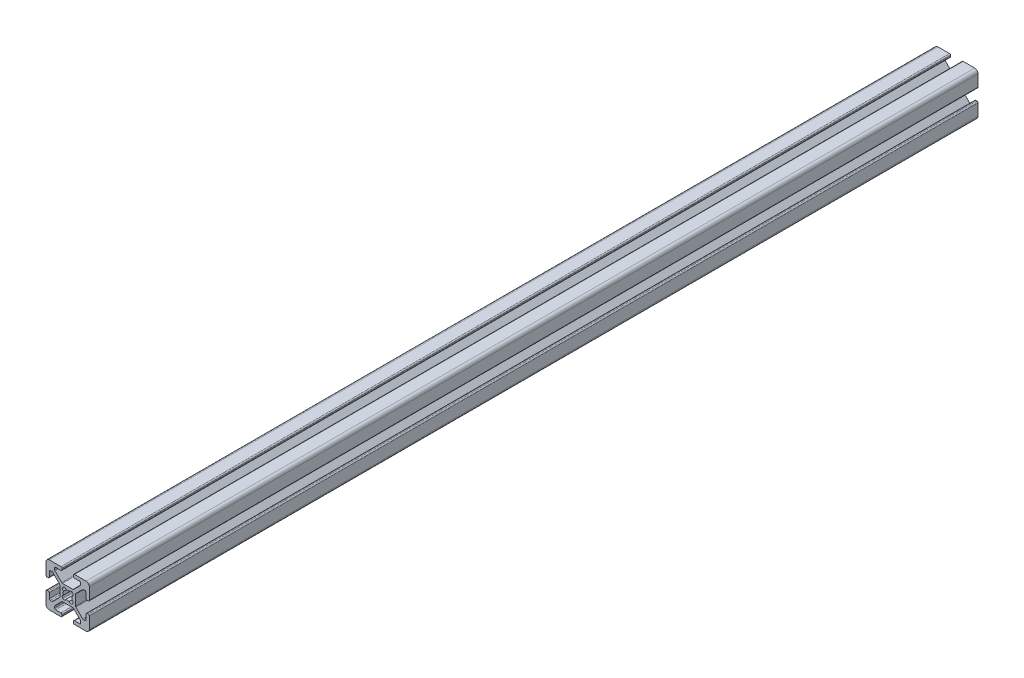
SolidWorks part; units mm, degrees
ref_plane "Front Plane" through (0, 0, 0) normal (0, 0, 1) x (1, 0, 0)
ref_plane "Top Plane" through (0, 0, 0) normal (0, 1, 0) x (1, 0, 0)
ref_plane "Right Plane" through (0, 0, 0) normal (1, 0, 0) x (0, 0, -1)
sketch "Sketch1" plane through (0, 0, 0) normal (0, 0, 1) x (1, 0, 0)
  line L0 (-5.0323, -0.3411) -> (-5.5163, -0.3411)
  line L1 (-6.0243, 0.1669) -> (-6.0243, 2.5159)
  line L2 (-4.5243, 0.1669) -> (-4.5243, 5.5289)
  line L3 (-10.8693, -5.355) -> (-10.8693, -0.5871)
  line L4 (-7.2582, 3.0239) -> (-6.5323, 3.0239)
  line L5 (-7.6174, 2.8752) -> (-10.7205, -0.2279)
  line L6 (-5.0323, -5.6011) -> (-5.5163, -5.6011)
  line L7 (-4.5243, -6.1091) -> (-4.5243, -11.4711)
  line L8 (-6.0243, -6.1091) -> (-6.0243, -8.4581)
  line L9 (-7.2582, -8.9661) -> (-6.5323, -8.9661)
  line L10 (-7.6174, -8.8173) -> (-10.7205, -5.7142)
  line L11 (-12.3994, -5.2756) -> (-12.2198, -5.096)
  line L12 (-17.1543, 6.5209) -> (-17.1543, 6.0369)
  line L13 (-17.6623, 7.0289) -> (-23.0243, 7.0289)
  line L14 (-17.6623, 5.5289) -> (-20.0113, 5.5289)
  line L15 (-12.1404, 0.6839) -> (-16.9082, 0.6839)
  line L16 (-20.5193, 4.295) -> (-20.5193, 5.0209)
  line L17 (-20.3705, 3.9358) -> (-17.2674, 0.8327)
  line L18 (-11.8943, 6.5209) -> (-11.8943, 6.0369)
  line L19 (-11.3863, 7.0289) -> (-6.0243, 7.0289)
  line L20 (-11.3863, 5.5289) -> (-9.0373, 5.5289)
  line L21 (-8.5293, 4.295) -> (-8.5293, 5.0209)
  line L22 (-8.6781, 3.9358) -> (-11.7812, 0.8327)
  line L23 (-12.2198, -0.8462) -> (-12.3994, -0.6666)
  line L24 (-24.0163, -5.6011) -> (-23.5323, -5.6011)
  line L25 (-24.5243, -6.1091) -> (-24.5243, -11.4711)
  line L26 (-23.0243, -6.1091) -> (-23.0243, -8.4581)
  line L27 (-18.1793, -0.5871) -> (-18.1793, -5.355)
  line L28 (-21.7904, -8.9661) -> (-22.5163, -8.9661)
  line L29 (-21.4312, -8.8173) -> (-18.3281, -5.7142)
  line L30 (-24.0163, -0.3411) -> (-23.5323, -0.3411)
  line L31 (-24.5243, 0.1669) -> (-24.5243, 5.5289)
  line L32 (-23.0243, 0.1669) -> (-23.0243, 2.5159)
  line L33 (-21.7904, 3.0239) -> (-22.5163, 3.0239)
  line L34 (-21.4312, 2.8752) -> (-18.3281, -0.2279)
  line L35 (-16.6492, -0.6666) -> (-16.8288, -0.8462)
  line L36 (-11.8943, -12.4631) -> (-11.8943, -11.9791)
  line L37 (-11.3863, -12.9711) -> (-6.0243, -12.9711)
  line L38 (-11.3863, -11.4711) -> (-9.0373, -11.4711)
  line L39 (-16.9082, -6.6261) -> (-12.1404, -6.6261)
  line L40 (-8.5293, -10.2371) -> (-8.5293, -10.9631)
  line L41 (-8.6781, -9.8779) -> (-11.7812, -6.7748)
  line L42 (-17.1543, -12.4631) -> (-17.1543, -11.9791)
  line L43 (-17.6623, -12.9711) -> (-23.0243, -12.9711)
  line L44 (-17.6623, -11.4711) -> (-20.0113, -11.4711)
  line L45 (-20.5193, -10.2371) -> (-20.5193, -10.9631)
  line L46 (-20.3705, -9.8779) -> (-17.2674, -6.7748)
  line L47 (-16.8288, -5.096) -> (-16.6492, -5.2756)
  arc A0 (-15.3283, -4.9062) -> (-13.7203, -4.9062) centre (-14.5243, -2.9711) ccw
  arc A1 (-6.0243, 2.5159) -> (-6.5323, 3.0239) centre (-6.5323, 2.5159) ccw
  arc A2 (-7.2582, 3.0239) -> (-7.6174, 2.8752) centre (-7.2582, 2.5159) ccw
  arc A3 (-10.7205, -0.2279) -> (-10.8693, -0.5871) centre (-10.3613, -0.5871) ccw
  arc A4 (-10.8693, -5.355) -> (-10.7205, -5.7142) centre (-10.3613, -5.355) ccw
  arc A5 (-7.6174, -8.8173) -> (-7.2582, -8.9661) centre (-7.2582, -8.4581) ccw
  arc A6 (-6.5323, -8.9661) -> (-6.0243, -8.4581) centre (-6.5323, -8.4581) ccw
  arc A7 (-5.5163, -5.6011) -> (-6.0243, -6.1091) centre (-5.5163, -6.1091) ccw
  arc A8 (-4.5243, -6.1091) -> (-5.0323, -5.6011) centre (-5.0323, -6.1091) ccw
  arc A9 (-5.0323, -0.3411) -> (-4.5243, 0.1669) centre (-5.0323, 0.1669) ccw
  arc A10 (-6.0243, 0.1669) -> (-5.5163, -0.3411) centre (-5.5163, 0.1669) ccw
  arc A11 (-13.7203, -4.9062) -> (-12.3994, -5.2756) centre (-12.9559, -4.7191) ccw
  arc A12 (-12.2198, -5.096) -> (-12.5892, -3.775) centre (-12.7763, -4.5395) ccw
  arc A13 (-17.1543, 6.5209) -> (-17.6623, 7.0289) centre (-17.6623, 6.5209) ccw
  arc A14 (-17.6623, 5.5289) -> (-17.1543, 6.0369) centre (-17.6623, 6.0369) ccw
  arc A15 (-12.5892, -3.775) -> (-12.5892, -2.1671) centre (-14.5243, -2.9711) ccw
  arc A16 (-17.2674, 0.8327) -> (-16.9082, 0.6839) centre (-16.9082, 1.1919) ccw
  arc A17 (-20.0113, 5.5289) -> (-20.5193, 5.0209) centre (-20.0113, 5.0209) ccw
  arc A18 (-20.5193, 4.295) -> (-20.3705, 3.9358) centre (-20.0113, 4.295) ccw
  arc A19 (-11.8943, 6.0369) -> (-11.3863, 5.5289) centre (-11.3863, 6.0369) ccw
  arc A20 (-11.3863, 7.0289) -> (-11.8943, 6.5209) centre (-11.3863, 6.5209) ccw
  arc A21 (-8.5293, 5.0209) -> (-9.0373, 5.5289) centre (-9.0373, 5.0209) ccw
  arc A22 (-8.6781, 3.9358) -> (-8.5293, 4.295) centre (-9.0373, 4.295) ccw
  arc A23 (-12.1404, 0.6839) -> (-11.7812, 0.8327) centre (-12.1404, 1.1919) ccw
  arc A24 (-12.5892, -2.1671) -> (-12.2198, -0.8462) centre (-12.7763, -1.4027) ccw
  arc A25 (-12.3994, -0.6666) -> (-13.7203, -1.0359) centre (-12.9559, -1.223) ccw
  arc A26 (-24.0163, -5.6011) -> (-24.5243, -6.1091) centre (-24.0163, -6.1091) ccw
  arc A27 (-23.0243, -6.1091) -> (-23.5323, -5.6011) centre (-23.5323, -6.1091) ccw
  arc A28 (-13.7203, -1.0359) -> (-15.3283, -1.0359) centre (-14.5243, -2.9711) ccw
  arc A29 (-18.3281, -5.7142) -> (-18.1793, -5.355) centre (-18.6873, -5.355) ccw
  arc A30 (-23.0243, -8.4581) -> (-22.5163, -8.9661) centre (-22.5163, -8.4581) ccw
  arc A31 (-21.7904, -8.9661) -> (-21.4312, -8.8173) centre (-21.7904, -8.4581) ccw
  arc A32 (-23.5323, -0.3411) -> (-23.0243, 0.1669) centre (-23.5323, 0.1669) ccw
  arc A33 (-24.5243, 0.1669) -> (-24.0163, -0.3411) centre (-24.0163, 0.1669) ccw
  arc A34 (-22.5163, 3.0239) -> (-23.0243, 2.5159) centre (-22.5163, 2.5159) ccw
  arc A35 (-21.4312, 2.8752) -> (-21.7904, 3.0239) centre (-21.7904, 2.5159) ccw
  arc A36 (-18.1793, -0.5871) -> (-18.3281, -0.2279) centre (-18.6873, -0.5871) ccw
  arc A37 (-15.3283, -1.0359) -> (-16.6492, -0.6666) centre (-16.0927, -1.223) ccw
  arc A38 (-16.8288, -0.8462) -> (-16.4594, -2.1671) centre (-16.2723, -1.4027) ccw
  arc A39 (-11.8943, -12.4631) -> (-11.3863, -12.9711) centre (-11.3863, -12.4631) ccw
  arc A40 (-11.3863, -11.4711) -> (-11.8943, -11.9791) centre (-11.3863, -11.9791) ccw
  arc A41 (-16.4594, -2.1671) -> (-16.4594, -3.775) centre (-14.5243, -2.9711) ccw
  arc A42 (-11.7812, -6.7748) -> (-12.1404, -6.6261) centre (-12.1404, -7.1341) ccw
  arc A43 (-9.0373, -11.4711) -> (-8.5293, -10.9631) centre (-9.0373, -10.9631) ccw
  arc A44 (-8.5293, -10.2371) -> (-8.6781, -9.8779) centre (-9.0373, -10.2371) ccw
  arc A45 (-17.1543, -11.9791) -> (-17.6623, -11.4711) centre (-17.6623, -11.9791) ccw
  arc A46 (-17.6623, -12.9711) -> (-17.1543, -12.4631) centre (-17.6623, -12.4631) ccw
  arc A47 (-20.5193, -10.9631) -> (-20.0113, -11.4711) centre (-20.0113, -10.9631) ccw
  arc A48 (-20.3705, -9.8779) -> (-20.5193, -10.2371) centre (-20.0113, -10.2371) ccw
  arc A49 (-16.9082, -6.6261) -> (-17.2674, -6.7748) centre (-16.9082, -7.1341) ccw
  arc A50 (-16.4594, -3.775) -> (-16.8288, -5.096) centre (-16.2723, -4.5395) ccw
  arc A51 (-16.6492, -5.2756) -> (-15.3283, -4.9062) centre (-16.0927, -4.7191) ccw
  arc A52 (-4.5243, 5.5289) -> (-6.0243, 7.0289) centre (-6.0243, 5.5289) ccw
  arc A53 (-6.0243, -12.9711) -> (-4.5243, -11.4711) centre (-6.0243, -11.4711) ccw
  arc A54 (-24.5243, -11.4711) -> (-23.0243, -12.9711) centre (-23.0243, -11.4711) ccw
  arc A55 (-23.0243, 7.0289) -> (-24.5243, 5.5289) centre (-23.0243, 5.5289) ccw
extrude "Extrude1" add sketch "Sketch1" along normal blind 410
